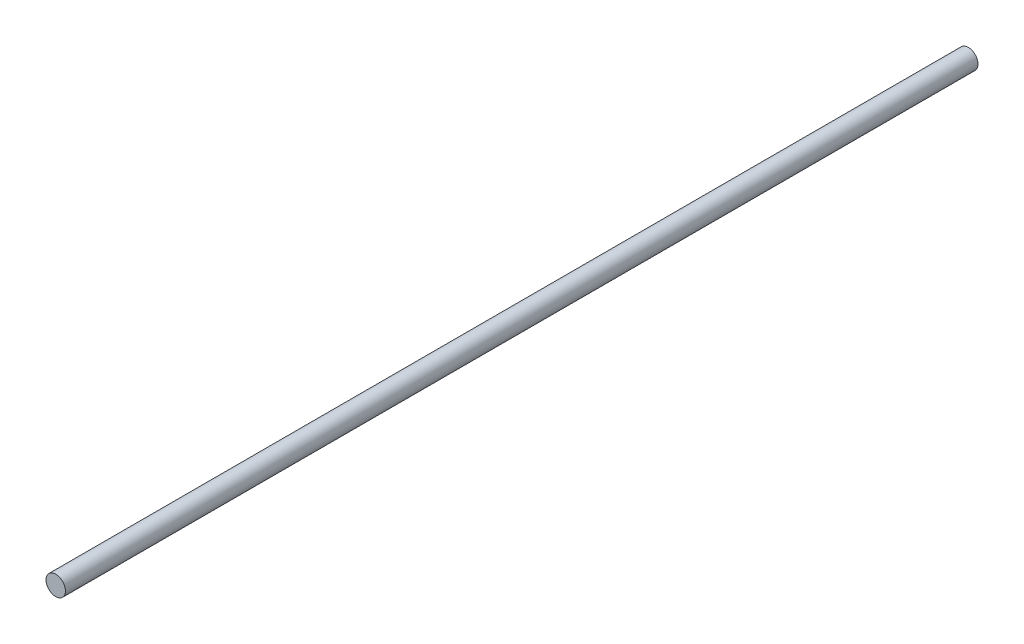
SolidWorks part; units mm, degrees
ref_plane "前视基准面" through (0, 0, 0) normal (0, 0, 1) x (1, 0, 0)
ref_plane "上视基准面" through (0, 0, 0) normal (0, 1, 0) x (1, 0, 0)
ref_plane "右视基准面" through (0, 0, 0) normal (1, 0, 0) x (0, 0, -1)
sketch "草图1" plane through (0, 0, 0) normal (0, 0, 1) x (1, 0, 0)
  circle A0 centre (0, 0) radius 4
  dimension "D1" = 8
extrude "凸台-拉伸1" add sketch "草图1" along normal blind 375
